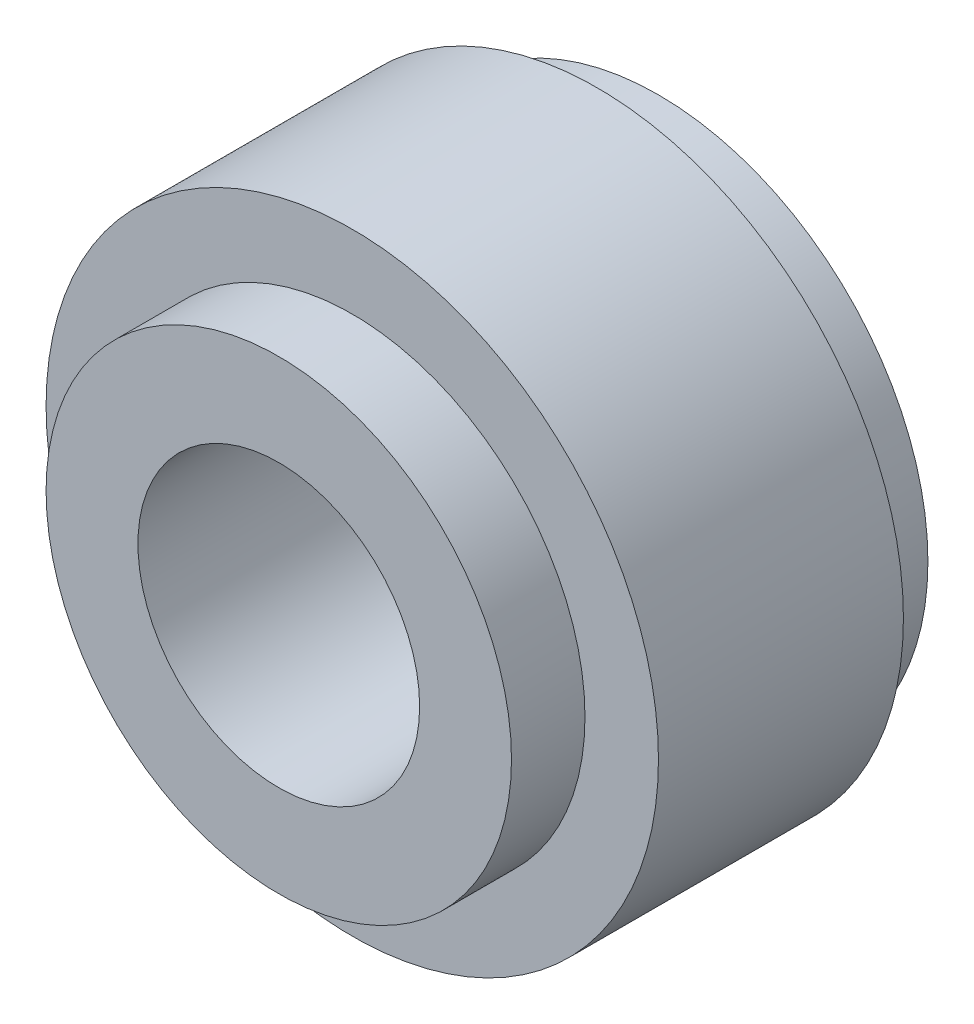
SolidWorks part; units mm, degrees
ref_plane "Front Plane" through (0, 0, 0) normal (0, 0, 1) x (1, 0, 0)
ref_plane "Top Plane" through (0, 0, 0) normal (0, 1, 0) x (1, 0, 0)
ref_plane "Right Plane" through (0, 0, 0) normal (1, 0, 0) x (0, 0, -1)
sketch "Sketch1" plane through (0, 0, 0) normal (0, 0, 1) x (1, 0, 0)
  circle A0 centre (0, 0) radius 25
  dimension "D1" = 50
extrude "Boss-Extrude1" add sketch "Sketch1" along normal blind 20
sketch "Sketch2" plane through (0, 0, 20) normal (0, 0, 1) x (1, 0, 0)
  circle A0 centre (0, 0) radius 19
  dimension "D1" = 38
extrude "Boss-Extrude2" add sketch "Sketch2" along normal blind 6
sketch "Sketch3" plane through (0, 0, 26) normal (0, 0, 1) x (1, 0, 0)
  circle A0 centre (0, 0) radius 11.5
  dimension "D1" = 23
extrude "Cut-Extrude1" cut sketch "Sketch3" against normal blind 60
sketch "Sketch5" plane through (0, 0, 0) normal (0, 0, -1) x (-1, 0, 0)
  circle A0 centre (0, 0) radius 22
  circle A1 centre (0, 0) radius 11.5
  dimension "D1" = 44
extrude "Boss-Extrude4" add sketch "Sketch5" along normal blind 5
